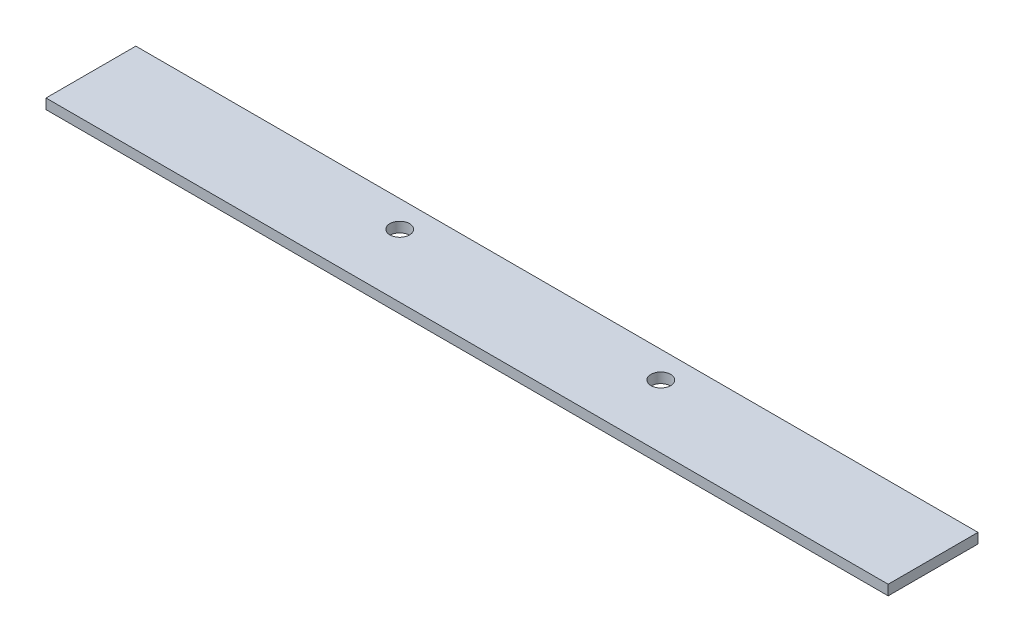
SolidWorks part; units mm, degrees
ref_plane "Alzado" through (0, 0, 0) normal (0, 0, 1) x (1, 0, 0)
ref_plane "Planta" through (0, 0, 0) normal (0, 1, 0) x (1, 0, 0)
ref_plane "Vista lateral" through (0, 0, 0) normal (1, 0, 0) x (0, 0, -1)
sketch "Croquis1" plane through (0, 0, 0) normal (0, 1, 0) x (1, 0, 0)
  line L1 (-75, -8) -> (75, -8)
  line L2 (-75, -8) -> (-75, 8)
  line L3 (-75, 8) -> (75, 8)
  line L4 (75, -8) -> (75, 8)
  line L5 (-75, -8) -> (75, 8) construction
  line L6 (-75, 8) -> (75, -8) construction
  point P0 (0, 0)
  dimension "D1" = 150
  dimension "D2" = 16
extrude "Saliente-Extruir1" add sketch "Croquis1" along normal blind 1.8
sketch "Croquis2" plane through (0, 1.8, 0) normal (0, 1, 0) x (1, 0, 0)
  line L0 (-23.25, 3.25) -> (23.25, 3.25) construction
  line L1 (75, 8) -> (-75, 8) construction
  circle A0 centre (-23.25, 3.25) radius 1.75
  circle A1 centre (23.25, 3.25) radius 1.75
  point P4 (0, 3.25)
  dimension "D1" = 3.5
  dimension "D2" = 46.5
  dimension "D3" = 4.75
extrude "Cortar-Extruir1" cut sketch "Croquis2" against normal through all
